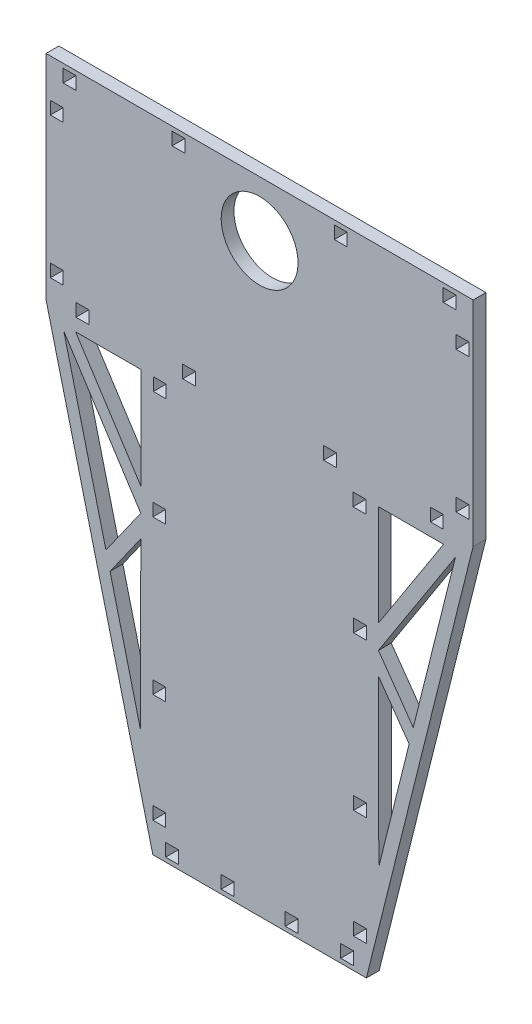
SolidWorks part; units mm, degrees
material "Pine"
ref_plane "정면" through (0, 0, 0) normal (0, 0, 1) x (1, 0, 0)
ref_plane "윗면" through (0, 0, 0) normal (0, 1, 0) x (1, 0, 0)
ref_plane "우측면" through (0, 0, 0) normal (1, 0, 0) x (0, 0, -1)
sketch "Sketch1" plane through (0, 0, 0) normal (0, 0, 1) x (1, 0, 0)
  line L0 (0, -33.3878) -> (0, 330.1576) construction
  line L5 (100, 300) -> (100, 200)
  line L6 (100, 200) -> (50, 0)
  line L7 (50, 0) -> (-50, 0)
  line L8 (-100, 300) -> (100, 300)
  line L9 (-100, 200) -> (-50, 0)
  line L10 (-100, 300) -> (-100, 200)
  line L11 (130.6916, 200) -> (43.0423, 200) construction
  point P9 (0, 300)
  point P10 (0, 0)
  point P11 (0, 300)
  point P12 (0, 0)
  dimension "D1" = 100
  dimension "D2" = 100
  dimension "D3" = 50
  dimension "D4" = 300
extrude "Boss-Extrude1" add sketch "Sketch1" along normal blind 6
sketch "Sketch4" plane through (0, 0, 0) normal (0, 0, -1) x (-1, 0, 0)
  line L0 (-252.2182, 250.3111) -> (-252.2182, 244.3111)
  line L1 (-252.2182, 244.3111) -> (-246.2182, 244.3111)
  line L2 (-246.2182, 244.3111) -> (-246.2182, 250.3111)
  line L3 (-246.2182, 250.3111) -> (-252.2182, 250.3111)
  line L4 (0, -23.7319) -> (0, 420.3937) construction
  line L5 (-98, 282) -> (-98, 276)
  line L6 (-98, 276) -> (-92, 276)
  line L7 (-92, 276) -> (-92, 282)
  line L8 (-92, 282) -> (-98, 282)
  line L13 (-98, 216) -> (-98, 210)
  line L14 (-98, 210) -> (-92, 210)
  line L15 (-92, 210) -> (-92, 216)
  line L16 (-92, 216) -> (-98, 216)
  line L17 (-92, 298) -> (-92, 292)
  line L18 (-92, 292) -> (-86, 292)
  line L19 (-86, 292) -> (-86, 298)
  line L20 (-86, 298) -> (-92, 298)
  line L21 (-44, 8) -> (-44, 2)
  line L22 (-44, 2) -> (-38, 2)
  line L23 (-38, 2) -> (-38, 8)
  line L24 (-38, 8) -> (-44, 8)
  line L25 (-100, 200) -> (-100, 300) construction
  line L26 (-100, 300) -> (100, 300) construction
  line L27 (-41, 298) -> (-41, 292)
  line L28 (-41, 292) -> (-35, 292)
  line L29 (-35, 292) -> (-35, 298)
  line L30 (-35, 298) -> (-41, 298)
  line L31 (-100, 200) -> (100, 200) construction
  line L34 (-86, 206) -> (-86, 200)
  line L35 (-86, 200) -> (-80, 200)
  line L36 (-80, 200) -> (-80, 206)
  line L37 (-80, 206) -> (-86, 206)
  line L38 (-66.3861, 200) -> (33.6139, 200) construction
  line L39 (-36, 206) -> (-36, 200)
  line L40 (-36, 200) -> (-30, 200)
  line L41 (-30, 200) -> (-30, 206)
  line L42 (-30, 206) -> (-36, 206)
  line L43 (50, 0) -> (-50, 0) construction
  line L44 (-18, 8) -> (-18, 2)
  line L45 (-18, 2) -> (-12, 2)
  line L46 (-12, 2) -> (-12, 8)
  line L47 (-12, 8) -> (-18, 8)
  line L56 (-115.4914, 40.7643) -> (120.5995, 40.7643) construction
  line L57 (-36, 26.0413) -> (-36, 163.8526) construction
  line L58 (-50, 20) -> (-44, 20)
  line L59 (-50, 14) -> (-50, 20)
  line L60 (-44, 14) -> (-50, 14)
  line L61 (-44, 20) -> (-44, 14)
  line L62 (-50, 0) -> (-50, 67.852) construction
  line L63 (-50, 71) -> (-44, 71)
  line L64 (-50, 65) -> (-50, 71)
  line L65 (-44, 65) -> (-50, 65)
  line L66 (-44, 71) -> (-44, 65)
  line L67 (-50, 19.2159) -> (-50, 220.6335) construction
  line L68 (-49.7488, 194) -> (-43.7488, 194)
  line L69 (-49.7488, 188) -> (-49.7488, 194)
  line L70 (-43.7488, 188) -> (-49.7488, 188)
  line L71 (-43.7488, 194) -> (-43.7488, 188)
  line L72 (-49.7488, 174) -> (-49.7488, 241.852) construction
  line L73 (-50, 143) -> (-44, 143)
  line L74 (-50, 137) -> (-50, 143)
  line L75 (-44, 137) -> (-50, 137)
  line L76 (-44, 143) -> (-44, 137)
  line L77 (-50, 142.4727) -> (-50, 210.3247) construction
  line L78 (35, 298) -> (41, 298)
  line L79 (35, 292) -> (35, 298)
  line L80 (41, 292) -> (35, 292)
  line L81 (41, 298) -> (41, 292)
  line L82 (86, 298) -> (92, 298)
  line L83 (86, 292) -> (86, 298)
  line L84 (92, 292) -> (86, 292)
  line L85 (92, 298) -> (92, 292)
  line L86 (92, 282) -> (98, 282)
  line L87 (92, 276) -> (92, 282)
  line L88 (98, 276) -> (92, 276)
  line L89 (98, 282) -> (98, 276)
  line L90 (80, 206) -> (86, 206)
  line L91 (80, 200) -> (80, 206)
  line L92 (86, 200) -> (80, 200)
  line L93 (86, 206) -> (86, 200)
  line L94 (92, 216) -> (98, 216)
  line L95 (92, 210) -> (92, 216)
  line L96 (98, 210) -> (92, 210)
  line L97 (98, 216) -> (98, 210)
  line L98 (49.7488, 174) -> (49.7488, 241.852) construction
  line L99 (43.7488, 194) -> (43.7488, 188)
  line L100 (43.7488, 188) -> (49.7488, 188)
  line L101 (49.7488, 188) -> (49.7488, 194)
  line L102 (49.7488, 194) -> (43.7488, 194)
  line L103 (44, 143) -> (44, 137)
  line L104 (44, 137) -> (50, 137)
  line L105 (50, 137) -> (50, 143)
  line L106 (50, 143) -> (44, 143)
  line L107 (44, 71) -> (44, 65)
  line L108 (44, 65) -> (50, 65)
  line L109 (50, 65) -> (50, 71)
  line L110 (50, 71) -> (44, 71)
  line L111 (44, 20) -> (44, 14)
  line L112 (44, 14) -> (50, 14)
  line L113 (50, 14) -> (50, 20)
  line L114 (50, 20) -> (44, 20)
  line L115 (38, 8) -> (44, 8)
  line L116 (38, 2) -> (38, 8)
  line L117 (44, 2) -> (38, 2)
  line L118 (44, 8) -> (44, 2)
  line L119 (12, 8) -> (18, 8)
  line L120 (12, 2) -> (12, 8)
  line L121 (18, 2) -> (12, 2)
  line L122 (18, 8) -> (18, 2)
  line L123 (66.3861, 200) -> (-33.6139, 200) construction
  line L124 (30, 206) -> (36, 206)
  line L125 (30, 200) -> (30, 206)
  line L126 (36, 200) -> (30, 200)
  line L127 (36, 206) -> (36, 200)
  line L128 (55.6221, 194) -> (86.1713, 194)
  line L129 (86.1713, 194) -> (55.6221, 146.7107)
  line L130 (55.6221, 146.7107) -> (55.6221, 194)
  line L131 (55.6401, 135.6812) -> (91.6847, 191.4772)
  line L140 (91.6847, 191.4772) -> (54.3218, 42.026) construction
  line L141 (91.6847, 191.4772) -> (71.9623, 112.588)
  line L142 (100, 200) -> (50, 0) construction
  line L143 (71.9623, 112.588) -> (55.6401, 135.6812)
  line L144 (55.6221, 197.4602) -> (55.6221, 31.1826) construction
  line L145 (70.0425, 104.9088) -> (55.6221, 125.3113)
  line L146 (55.6221, 125.3113) -> (55.8322, 48.0673)
  line L147 (55.8322, 48.0673) -> (70.0425, 104.9088)
  line L148 (-55.8322, 48.0673) -> (-70.0425, 104.9088)
  line L149 (-55.6221, 125.3113) -> (-55.8322, 48.0673)
  line L150 (-70.0425, 104.9088) -> (-55.6221, 125.3113)
  line L151 (-71.9623, 112.588) -> (-55.6401, 135.6812)
  line L152 (-91.6847, 191.4772) -> (-71.9623, 112.588)
  line L153 (-55.6401, 135.6812) -> (-91.6847, 191.4772)
  line L154 (-86.1713, 194) -> (-55.6221, 146.7107)
  line L155 (-55.6221, 146.7107) -> (-55.6221, 194)
  line L156 (-55.6221, 194) -> (-86.1713, 194)
  point P27 (-92, 295)
  point P32 (-41, 295)
  point P33 (-95, 282)
  point P34 (-98, 213)
  point P98 (0, 200)
  dimension "D1" = 6
  dimension "D2" = 6
  dimension "D3" = 2
  dimension "D4" = 2
  dimension "D5" = 8
  dimension "D6" = 6
  dimension "D7" = 2
  dimension "D8" = 45
  dimension "D9" = 6
  dimension "D10" = 6
  dimension "D11" = 6
  dimension "D12" = 10
  dimension "D13" = 10
  dimension "D14" = 2
  dimension "D15" = 6
  dimension "D16" = 6
  dimension "D17" = 6
  dimension "D18" = 6
  dimension "D19" = 6
  dimension "D20" = 6
  dimension "D21" = 14
  dimension "D22" = 6
  dimension "D23" = 6
  dimension "D24" = 44
  dimension "D25" = 2
  dimension "D26" = 6
  dimension "D27" = 6
  dimension "D28" = 6
  dimension "D29" = 6
  dimension "D30" = 6
  dimension "D31" = 20
  dimension "D32" = 90
  dimension "D33" = 6
  dimension "D34" = 6
  dimension "D35" = 14
  dimension "D36" = 6
  dimension "D37" = 6
  dimension "D38" = 45
  dimension "D39" = 6
  dimension "D40" = 6
  dimension "D41" = 6
  dimension "D42" = 6
  dimension "D43" = 6
  dimension "D44" = 45
  dimension "D45" = 6
  dimension "D46" = 6
  dimension "D47" = 6
extrude "Cut-Extrude2" cut sketch "Sketch4" against normal blind 6
sketch "Sketch5" plane through (0, 0, 0) normal (0, 0, -1) x (-1, 0, 0)
  line L0 (-86, 292) -> (86, 292) construction
  circle A0 centre (0, 274) radius 18
extrude "Cut-Extrude3" cut sketch "Sketch5" against normal blind 6 contours A0
